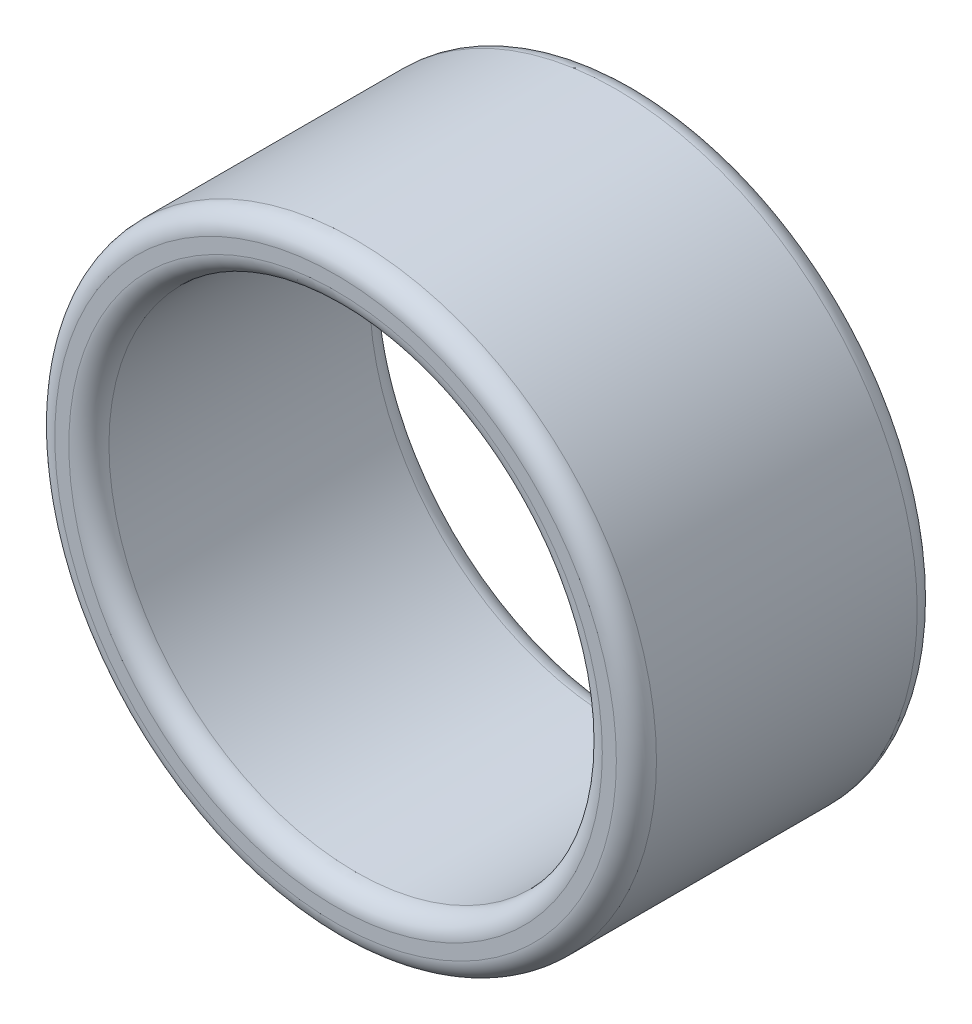
SolidWorks part; units mm, degrees
ref_plane "Front Plane" through (0, 0, 0) normal (0, 0, 1) x (1, 0, 0)
ref_plane "Top Plane" through (0, 0, 0) normal (0, 1, 0) x (1, 0, 0)
ref_plane "Right Plane" through (0, 0, 0) normal (1, 0, 0) x (0, 0, -1)
other "Bounding Box"
ref_plane "Default Plane" through (13.8565, 3.175, 6.7999) normal (0, -1, 0) x (-1, 0, 0)
sketch "Sketch1" plane through (0, 0, 0) normal (0, 0, 1) x (1, 0, 0)
  circle A0 centre (0, 0) radius 1.5621
  circle A1 centre (0, 0) radius 1.905
  dimension "D1" = 3.1242
  dimension "D2" = 3.81
extrude "Boss-Extrude1" add sketch "Sketch1" along normal blind 1.905
fillet "Fillet1" radius 0.127 4 edges at (1.5621, 0, 1.905) (1.905, 0, 1.905) (1.5621, 0, 0) (1.905, 0, 0)
